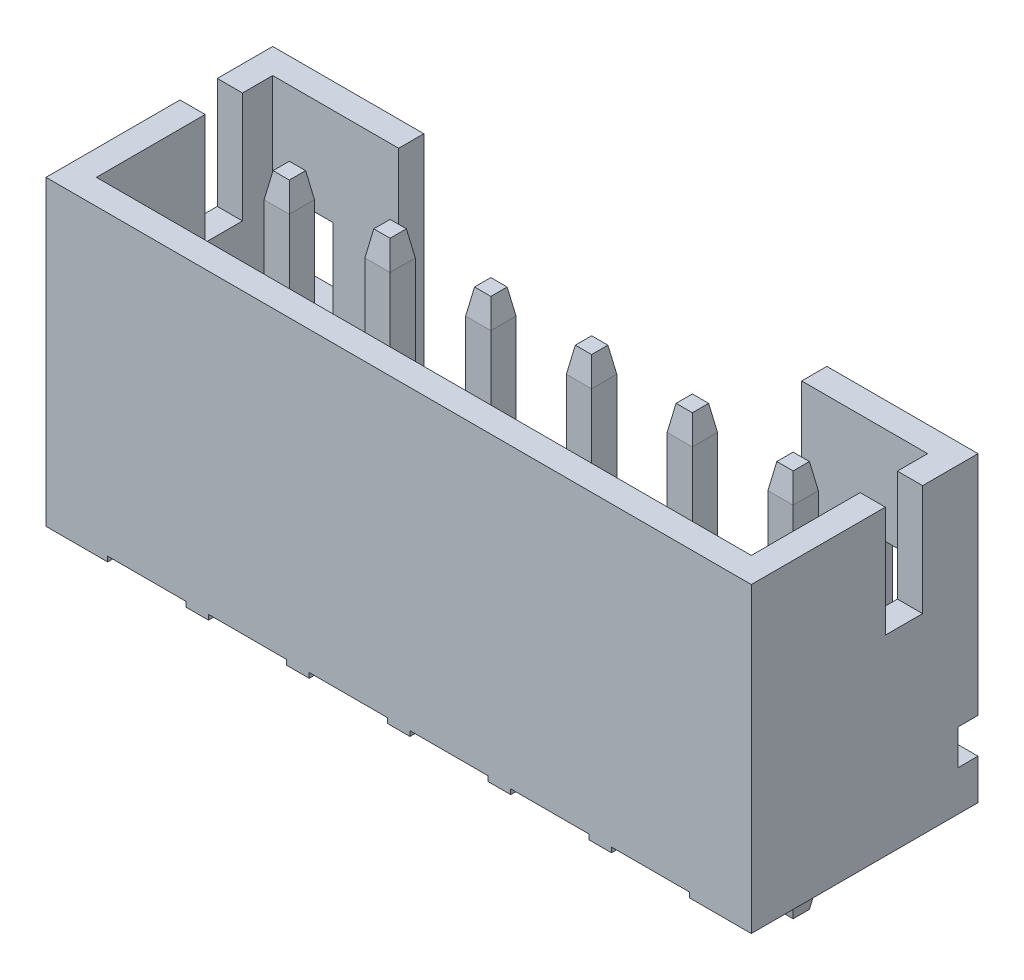
SolidWorks part; units mm, degrees
ref_plane "Front Plane" through (0, 0, 0) normal (0, 0, 1) x (1, 0, 0)
ref_plane "Top Plane" through (0, 0, 0) normal (0, 1, 0) x (1, 0, 0)
ref_plane "Right Plane" through (0, 0, 0) normal (1, 0, 0) x (0, 0, -1)
sketch "Sketch1" plane through (0, 0, 0) normal (0, 1, 0) x (1, 0, 0)
  line L1 (-8, 2.25) -> (6, 2.25)
  line L2 (-8, 2.25) -> (-8, -2.25)
  line L3 (-8, -2.25) -> (6, -2.25)
  line L4 (6, 2.25) -> (6, -2.25)
  dimension "D1" = 14
  dimension "D2" = 4.5
  dimension "D3" = 2.25
  dimension "D4" = 6
extrude "Extrude1" add sketch "Sketch1" along normal blind 6
sketch "Sketch2" plane through (0, 0, 2.25) normal (0, 0, 1) x (1, 0, 0)
  line L0 (-8, 0) -> (6, 0) construction
  line L6 (-0.775, 0.1) -> (0.775, 0.1)
  line L7 (-0.775, 0.1) -> (-0.775, 0)
  line L8 (-0.775, 0) -> (0, 0)
  line L9 (0.775, 0.1) -> (0.775, 0)
  line L10 (0, 0) -> (0.775, 0)
  dimension "D1" = 0.1
  dimension "D3" = 1.55
extrude "Cut-Extrude1" cut sketch "Sketch2" against normal through all
sketch "Sketch3" plane through (0, 6, 0) normal (0, 1, 0) x (-1, 0, 0)
  line L0 (-6, -2.25) -> (8, -2.25) construction
  line L1 (7.5, -1.75) -> (-5.5, -1.75)
  line L2 (7.5, -1.75) -> (7.5, 1.75)
  line L3 (7.5, 1.75) -> (-5.5, 1.75)
  line L4 (-5.5, -1.75) -> (-5.5, 1.75)
  line L5 (8, 2.25) -> (-6, 2.25) construction
  line L6 (-6, 2.25) -> (-6, -2.25) construction
  line L7 (8, -2.25) -> (8, 2.25) construction
  dimension "D1" = 0.5
  dimension "D2" = 0.5
  dimension "D3" = 0.5
  dimension "D4" = 0.5
extrude "Cut-Extrude2" cut sketch "Sketch3" against normal offset from surface (4.2 mm away) 1.8 up to face at (3.3875, 0, 0)
sketch "Sketch5" plane through (-8, 0, 0) normal (-1, 0, 0) x (0, 0, 1)
  line L1 (-1.15, 6) -> (-0.41, 6)
  line L2 (-1.15, 6) -> (-1.15, 3.8)
  line L3 (-1.15, 3.8) -> (-0.41, 3.8)
  line L4 (-0.41, 6) -> (-0.41, 3.8)
  line L5 (-2.25, 6) -> (-2.25, 0) construction
  line L6 (-2.25, 6) -> (2.25, 6) construction
  dimension "D1" = 2.2
  dimension "D2" = 0.74
  dimension "D3" = 1.1
extrude "Cut-Extrude3" cut sketch "Sketch5" against normal through all
sketch "Sketch6" plane through (0, 0, -2.25) normal (0, 0, -1) x (-1, 0, 0)
  line L1 (-6, 6) -> (8, 6) construction
  line L2 (-3, 6) -> (5, 6)
  line L3 (-3, 6) -> (-3, 2)
  line L4 (-3, 2) -> (5, 2)
  line L5 (5, 6) -> (5, 2)
  dimension "D1" = 8
  dimension "D2" = 3
  dimension "D3" = 4
extrude "Cut-Extrude4" cut sketch "Sketch6" against normal blind 1.2
ref_plane "Plane1" through (0, 8.5, 0) normal (0, 1, 0) x (-1, 0, 0)
sketch "Sketch8" plane through (0, 8.5, 0) normal (0, 1, 0) x (-1, 0, 0)
  line L0 (-6, 2.25) -> (-6, -2.25) construction
  line L1 (8, -2.25) -> (8, 2.25) construction
  line L2 (-6, 2.25) -> (-6, -2.25)
  line L3 (8, -2.25) -> (8, 2.25)
  line L4 (-6, 2.25) -> (8, 2.25)
  line L5 (8, -2.25) -> (-6, -2.25)
sketch "Sketch9" plane through (0, 0, 0) normal (1, 0, 0) x (0, 0, -1)
  line L0 (2.25, 6) -> (2.25, 0) construction
  line L1 (2.25, 1.5) -> (1.85, 1.5)
  line L2 (2.25, 1.5) -> (2.25, 0.8)
  line L3 (2.25, 0.8) -> (1.85, 0.8)
  line L4 (1.85, 1.5) -> (1.85, 0.8)
  line L5 (2.25, 0) -> (-2.25, 0) construction
  line L6 (-2.25, 6) -> (-2.25, 0) construction
  dimension "D1" = 0.8
  dimension "D2" = 0.7
  dimension "D3" = 4.1
extrude "Cut-Extrude5" cut sketch "Sketch9" against normal through all and the other way through all
sketch "Sketch10" plane through (0, 0, -2.25) normal (0, 0, -1) x (-1, 0, 0)
  line L0 (-5.5, 1.8) -> (-5.5, 6) construction
  line L1 (-5.5, 4.0716) -> (-4.3, 4.0716)
  line L2 (-5.5, 4.0716) -> (-5.5, 2.4716)
  line L3 (-5.5, 2.4716) -> (-4.3, 2.4716)
  line L4 (-4.3, 4.0716) -> (-4.3, 2.4716)
  line L5 (7.5, 1.8) -> (7.5, 6) construction
  line L6 (7.5, 4.0716) -> (6.3, 4.0716)
  line L7 (7.5, 4.0716) -> (7.5, 2.4716)
  line L8 (7.5, 2.4716) -> (6.3, 2.4716)
  line L9 (6.3, 4.0716) -> (6.3, 2.4716)
  dimension "D1" = 1.2
  dimension "D2" = 1.6
extrude "Cut-Extrude6" cut sketch "Sketch10" against normal up to surface (0.5 mm away) up to face at (-1, 3.95, -1.75)
sketch "Sketch11" plane through (0, 0, 0) normal (1, 0, 0) x (0, 0, -1)
  line L0 (0, 1.8) -> (-0.5764, 1.2236)
  line L1 (-1.75, 1.8) -> (1.75, 1.8) construction
  line L2 (-0.5764, 1.2236) -> (-1.75, 1.2236)
  line L3 (-1.75, 1.2236) -> (-1.75, 1.8)
  line L4 (-1.75, 1.8) -> (0, 1.8)
extrude "Cut-Extrude7" cut sketch "Sketch11" against normal up to surface and the other way up to surface
pattern_linear "LPattern4" count 3 spacing 2 along (1, 0, 0) count 4 spacing 2 along (-1, 0, 0) of "Cut-Extrude1"
sketch "Sketch7" plane through (0, 0, 0) normal (0, 1, 0) x (1, 0, 0)
  line L0 (0, 0.33) -> (0.25, 0.33)
  line L1 (-0.25, 0.33) -> (0, 0.33)
  line L2 (-0.25, 0.33) -> (-0.25, 0.83)
  line L3 (-0.25, 0.83) -> (0.25, 0.83)
  line L4 (0.25, 0.33) -> (0.25, 0.83)
  line L5 (0.775, 2.25) -> (-0.775, 2.25) construction
  dimension "D1" = 0.5
  dimension "D2" = 0.5
  dimension "D3" = 1.42
extrude "Extrude2" add sketch "Sketch7" along normal offset from surface 0.3 and the other way blind 2 up to face at (-1, 6, 0.795)
pattern_linear "LPattern2" count 3 spacing 2 along (1, 0, 0) count 4 spacing 2 along (-1, 0, 0) of "Extrude2"
chamfer "Chamfer1" distance 0.5 angle 10 48 edges at (0, -2, -0.33) (0.25, -2, -0.58) (0, -2, -0.83) (-0.25, -2, -0.58) (0.25, 5.7, -0.58) (0, 5.7, -0.33) (-0.25, 5.7, -0.58) (0, 5.7, -0.83) (4.25, 5.7, -0.58) (4, 5.7, -0.83) (4, 5.7, -0.33) (3.75, 5.7, -0.58) (-3.75, 5.7, -0.58) (-4, 5.7, -0.83) (-4, 5.7, -0.33) (-4.25, 5.7, -0.58) (-1.75, 5.7, -0.58) (-2, 5.7, -0.83) (-2, 5.7, -0.33) (-2.25, 5.7, -0.58) (2.25, 5.7, -0.58) (2, 5.7, -0.83) (2, 5.7, -0.33) (1.75, 5.7, -0.58) (4, -2, -0.83) (4, -2, -0.33) (4.25, -2, -0.58) (3.75, -2, -0.58) (2, -2, -0.83) (2, -2, -0.33) (2.25, -2, -0.58) (1.75, -2, -0.58) (-2, -2, -0.83) (-2, -2, -0.33) (-1.75, -2, -0.58) (-2.25, -2, -0.58) (-4, -2, -0.83) (-4, -2, -0.33) (-3.75, -2, -0.58) (-4.25, -2, -0.58) (-6, -2, -0.83) (-6, -2, -0.33) (-5.75, -2, -0.58) (-6.25, -2, -0.58) (-5.75, 5.7, -0.58) (-6, 5.7, -0.83) (-6, 5.7, -0.33) (-6.25, 5.7, -0.58)
sketch "Component_Outline" plane through (0, 0, 0) normal (0, 1, 0) x (1, 0, 0)
  line L0 (-8, 2.25) -> (6, -2.25) construction
  line L1 (6, -2.25) -> (-8, -2.25)
  line L2 (6, -2.25) -> (6, 2.25)
  line L3 (6, 2.25) -> (-8, 2.25)
  line L4 (-8, -2.25) -> (-8, 2.25)
  point P6 (-1, 0)
